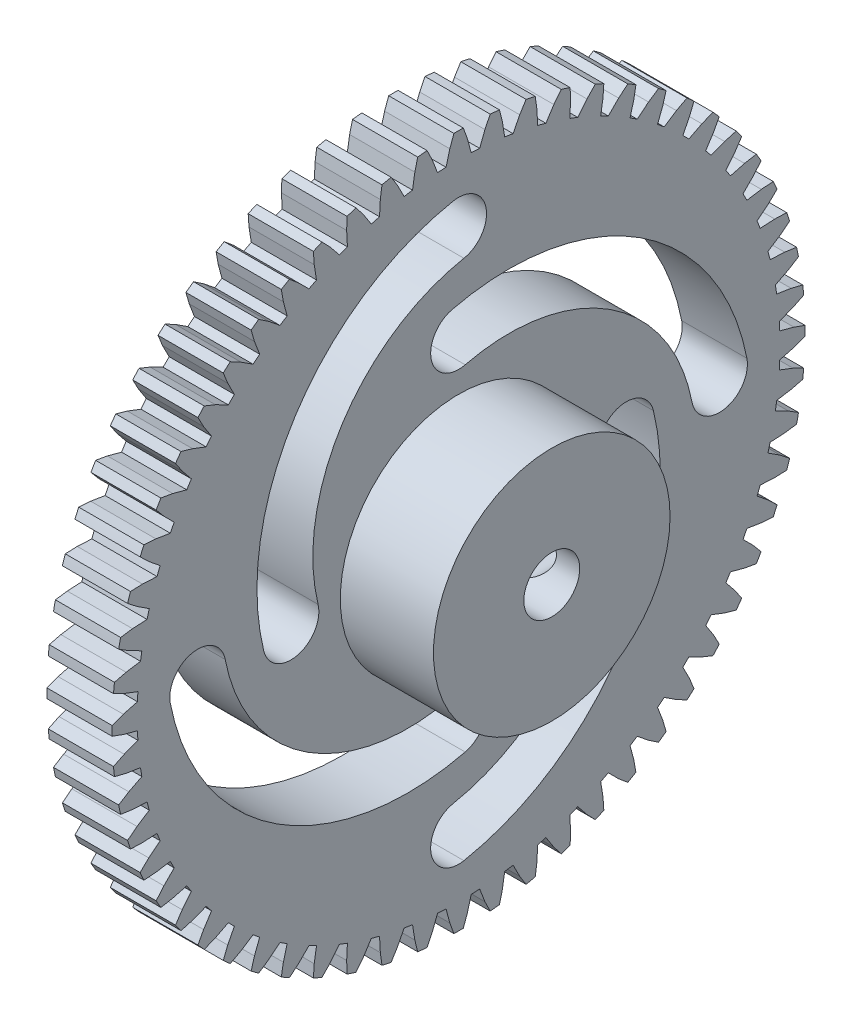
SolidWorks part; units mm, degrees
ref_plane "Front Plane" through (0, 0, 0) normal (0, 0, 1) x (1, 0, 0)
ref_plane "Top Plane" through (0, 0, 0) normal (0, 1, 0) x (1, 0, 0)
ref_plane "Right Plane" through (0, 0, 0) normal (1, 0, 0) x (0, 0, -1)
ref_plane "Plane1" through (6, 0, 0) normal (1, 0, 0) x (0, 0, -1)
sketch "Sketch1" plane through (6, 0, 0) normal (1, 0, 0) x (0, 0, -1)
  line L0 (1.6942, 18.5227) -> (1.4122, 17.9445)
  line L1 (-0.2512, 18.5983) -> (-0.4712, 17.9938)
  line L2 (-0.4712, 17.9938) -> (-0.6741, 17.2368)
  line L3 (-1.1314, 17.2129) -> (-1.4122, 17.9445)
  line L4 (-1.4122, 17.9445) -> (-1.6942, 18.5227)
  line L5 (1.4122, 17.9445) -> (1.1314, 17.2129)
  line L6 (0.6741, 17.2368) -> (0.4712, 17.9938)
  line L7 (0.4712, 17.9938) -> (0.2512, 18.5983)
  line L8 (3.6211, 18.2441) -> (3.2802, 17.6986)
  line L9 (3.2802, 17.6986) -> (2.9244, 17.0003)
  line L10 (2.4721, 17.0719) -> (2.3495, 17.846)
  line L11 (2.3495, 17.846) -> (2.1939, 18.4702)
  line L12 (5.5083, 17.7657) -> (5.1122, 17.2588)
  line L13 (5.1122, 17.2588) -> (4.6854, 16.6015)
  line L14 (4.2431, 16.72) -> (4.2021, 17.5026)
  line L15 (4.2021, 17.5026) -> (4.1125, 18.1397)
  line L16 (7.3351, 17.0926) -> (6.8883, 16.6299)
  line L17 (6.8883, 16.6299) -> (6.395, 16.0208)
  line L18 (5.9676, 16.1849) -> (6.0086, 16.9675)
  line L19 (6.0086, 16.9675) -> (5.9861, 17.6104)
  line L20 (9.0816, 16.2322) -> (8.5888, 15.8187)
  line L21 (8.5888, 15.8187) -> (8.0346, 15.2646)
  line L22 (7.6266, 15.4725) -> (7.7492, 16.2465)
  line L23 (7.7492, 16.2465) -> (7.7941, 16.8882)
  line L24 (10.7286, 15.194) -> (10.1953, 14.8343)
  line L25 (10.1953, 14.8343) -> (9.5862, 14.3411)
  line L26 (9.2022, 14.5905) -> (9.405, 15.3475)
  line L27 (9.405, 15.3475) -> (9.5167, 15.981)
  line L28 (12.258, 13.9893) -> (11.69, 13.6873)
  line L29 (11.69, 13.6873) -> (11.0327, 13.2605)
  line L30 (10.6769, 13.5487) -> (10.9577, 14.2803)
  line L31 (10.9577, 14.2803) -> (11.1351, 14.8987)
  line L32 (13.6531, 12.6314) -> (13.0567, 12.3904)
  line L33 (13.0567, 12.3904) -> (12.3584, 12.0346)
  line L34 (12.0346, 12.3584) -> (12.3904, 13.0567)
  line L35 (12.3904, 13.0567) -> (12.6314, 13.6531)
  line L36 (14.8987, 11.1351) -> (14.2803, 10.9577)
  line L37 (14.2803, 10.9577) -> (13.5487, 10.6769)
  line L38 (13.2605, 11.0327) -> (13.6873, 11.69)
  line L39 (13.6873, 11.69) -> (13.9893, 12.258)
  line L40 (15.981, 9.5167) -> (15.3475, 9.405)
  line L41 (15.3475, 9.405) -> (14.5905, 9.2022)
  line L42 (14.3411, 9.5862) -> (14.8343, 10.1953)
  line L43 (14.8343, 10.1953) -> (15.194, 10.7286)
  line L44 (16.8882, 7.7941) -> (16.2465, 7.7492)
  line L45 (16.2465, 7.7492) -> (15.4725, 7.6266)
  line L46 (15.2646, 8.0346) -> (15.8187, 8.5888)
  line L47 (15.8187, 8.5888) -> (16.2322, 9.0816)
  line L48 (17.6104, 5.9861) -> (16.9675, 6.0086)
  line L49 (16.9675, 6.0086) -> (16.1849, 5.9676)
  line L50 (16.0208, 6.395) -> (16.6299, 6.8883)
  line L51 (16.6299, 6.8883) -> (17.0926, 7.3351)
  line L52 (18.1397, 4.1125) -> (17.5026, 4.2021)
  line L53 (17.5026, 4.2021) -> (16.72, 4.2431)
  line L54 (16.6015, 4.6854) -> (17.2588, 5.1122)
  line L55 (17.2588, 5.1122) -> (17.7657, 5.5083)
  line L56 (18.4702, 2.1939) -> (17.846, 2.3495)
  line L57 (17.846, 2.3495) -> (17.0719, 2.4721)
  line L58 (17.0003, 2.9244) -> (17.6986, 3.2802)
  line L59 (17.6986, 3.2802) -> (18.2441, 3.6211)
  line L60 (18.5983, 0.2512) -> (17.9938, 0.4712)
  line L61 (17.9938, 0.4712) -> (17.2368, 0.6741)
  line L62 (17.2129, 1.1314) -> (17.9445, 1.4122)
  line L63 (17.9445, 1.4122) -> (18.5227, 1.6942)
  line L64 (18.5227, -1.6942) -> (17.9445, -1.4122)
  line L65 (17.9445, -1.4122) -> (17.2129, -1.1314)
  line L66 (17.2368, -0.6741) -> (17.9938, -0.4712)
  line L67 (17.9938, -0.4712) -> (18.5983, -0.2512)
  line L68 (18.2441, -3.6211) -> (17.6986, -3.2802)
  line L69 (17.6986, -3.2802) -> (17.0003, -2.9244)
  line L70 (17.0719, -2.4721) -> (17.846, -2.3495)
  line L71 (17.846, -2.3495) -> (18.4702, -2.1939)
  line L72 (17.7657, -5.5083) -> (17.2588, -5.1122)
  line L73 (17.2588, -5.1122) -> (16.6015, -4.6854)
  line L74 (16.72, -4.2431) -> (17.5026, -4.2021)
  line L75 (17.5026, -4.2021) -> (18.1397, -4.1125)
  line L76 (17.0926, -7.3351) -> (16.6299, -6.8883)
  line L77 (16.6299, -6.8883) -> (16.0208, -6.395)
  line L78 (16.1849, -5.9676) -> (16.9675, -6.0086)
  line L79 (16.9675, -6.0086) -> (17.6104, -5.9861)
  line L80 (16.2322, -9.0816) -> (15.8187, -8.5888)
  line L81 (15.8187, -8.5888) -> (15.2646, -8.0346)
  line L82 (15.4725, -7.6266) -> (16.2465, -7.7492)
  line L83 (16.2465, -7.7492) -> (16.8882, -7.7941)
  line L84 (15.194, -10.7286) -> (14.8343, -10.1953)
  line L85 (14.8343, -10.1953) -> (14.3411, -9.5862)
  line L86 (14.5905, -9.2022) -> (15.3475, -9.405)
  line L87 (15.3475, -9.405) -> (15.981, -9.5167)
  line L88 (13.9893, -12.258) -> (13.6873, -11.69)
  line L89 (13.6873, -11.69) -> (13.2605, -11.0327)
  line L90 (13.5487, -10.6769) -> (14.2803, -10.9577)
  line L91 (14.2803, -10.9577) -> (14.8987, -11.1351)
  line L92 (12.6314, -13.6531) -> (12.3904, -13.0567)
  line L93 (12.3904, -13.0567) -> (12.0346, -12.3584)
  line L94 (12.3584, -12.0346) -> (13.0567, -12.3904)
  line L95 (13.0567, -12.3904) -> (13.6531, -12.6314)
  line L96 (11.1351, -14.8987) -> (10.9577, -14.2803)
  line L97 (10.9577, -14.2803) -> (10.6769, -13.5487)
  line L98 (11.0327, -13.2605) -> (11.69, -13.6873)
  line L99 (11.69, -13.6873) -> (12.258, -13.9893)
  line L100 (9.5167, -15.981) -> (9.405, -15.3475)
  line L101 (9.405, -15.3475) -> (9.2022, -14.5905)
  line L102 (9.5862, -14.3411) -> (10.1953, -14.8343)
  line L103 (10.1953, -14.8343) -> (10.7286, -15.194)
  line L104 (7.7941, -16.8882) -> (7.7492, -16.2465)
  line L105 (7.7492, -16.2465) -> (7.6266, -15.4725)
  line L106 (8.0346, -15.2646) -> (8.5888, -15.8187)
  line L107 (8.5888, -15.8187) -> (9.0816, -16.2322)
  line L108 (5.9861, -17.6104) -> (6.0086, -16.9675)
  line L109 (6.0086, -16.9675) -> (5.9676, -16.1849)
  line L110 (6.395, -16.0208) -> (6.8883, -16.6299)
  line L111 (6.8883, -16.6299) -> (7.3351, -17.0926)
  line L112 (4.1125, -18.1397) -> (4.2021, -17.5026)
  line L113 (4.2021, -17.5026) -> (4.2431, -16.72)
  line L114 (4.6854, -16.6015) -> (5.1122, -17.2588)
  line L115 (5.1122, -17.2588) -> (5.5083, -17.7657)
  line L116 (2.1939, -18.4702) -> (2.3495, -17.846)
  line L117 (2.3495, -17.846) -> (2.4721, -17.0719)
  line L118 (2.9244, -17.0003) -> (3.2802, -17.6986)
  line L119 (3.2802, -17.6986) -> (3.6211, -18.2441)
  line L120 (0.2512, -18.5983) -> (0.4712, -17.9938)
  line L121 (0.4712, -17.9938) -> (0.6741, -17.2368)
  line L122 (1.1314, -17.2129) -> (1.4122, -17.9445)
  line L123 (1.4122, -17.9445) -> (1.6942, -18.5227)
  line L124 (-1.6942, -18.5227) -> (-1.4122, -17.9445)
  line L125 (-1.4122, -17.9445) -> (-1.1314, -17.2129)
  line L126 (-0.6741, -17.2368) -> (-0.4712, -17.9938)
  line L127 (-0.4712, -17.9938) -> (-0.2512, -18.5983)
  line L128 (-3.6211, -18.2441) -> (-3.2802, -17.6986)
  line L129 (-3.2802, -17.6986) -> (-2.9244, -17.0003)
  line L130 (-2.4721, -17.0719) -> (-2.3495, -17.846)
  line L131 (-2.3495, -17.846) -> (-2.1939, -18.4702)
  line L132 (-5.5083, -17.7657) -> (-5.1122, -17.2588)
  line L133 (-5.1122, -17.2588) -> (-4.6854, -16.6015)
  line L134 (-4.2431, -16.72) -> (-4.2021, -17.5026)
  line L135 (-4.2021, -17.5026) -> (-4.1125, -18.1397)
  line L136 (-7.3351, -17.0926) -> (-6.8883, -16.6299)
  line L137 (-6.8883, -16.6299) -> (-6.395, -16.0208)
  line L138 (-5.9676, -16.1849) -> (-6.0086, -16.9675)
  line L139 (-6.0086, -16.9675) -> (-5.9861, -17.6104)
  line L140 (-9.0816, -16.2322) -> (-8.5888, -15.8187)
  line L141 (-8.5888, -15.8187) -> (-8.0346, -15.2646)
  line L142 (-7.6266, -15.4725) -> (-7.7492, -16.2465)
  line L143 (-7.7492, -16.2465) -> (-7.7941, -16.8882)
  line L144 (-10.7286, -15.194) -> (-10.1953, -14.8343)
  line L145 (-10.1953, -14.8343) -> (-9.5862, -14.3411)
  line L146 (-9.2022, -14.5905) -> (-9.405, -15.3475)
  line L147 (-9.405, -15.3475) -> (-9.5167, -15.981)
  line L148 (-12.258, -13.9893) -> (-11.69, -13.6873)
  line L149 (-11.69, -13.6873) -> (-11.0327, -13.2605)
  line L150 (-10.6769, -13.5487) -> (-10.9577, -14.2803)
  line L151 (-10.9577, -14.2803) -> (-11.1351, -14.8987)
  line L152 (-13.6531, -12.6314) -> (-13.0567, -12.3904)
  line L153 (-13.0567, -12.3904) -> (-12.3584, -12.0346)
  line L154 (-12.0346, -12.3584) -> (-12.3904, -13.0567)
  line L155 (-12.3904, -13.0567) -> (-12.6314, -13.6531)
  line L156 (-14.8987, -11.1351) -> (-14.2803, -10.9577)
  line L157 (-14.2803, -10.9577) -> (-13.5487, -10.6769)
  line L158 (-13.2605, -11.0327) -> (-13.6873, -11.69)
  line L159 (-13.6873, -11.69) -> (-13.9893, -12.258)
  line L160 (-15.981, -9.5167) -> (-15.3475, -9.405)
  line L161 (-15.3475, -9.405) -> (-14.5905, -9.2022)
  line L162 (-14.3411, -9.5862) -> (-14.8343, -10.1953)
  line L163 (-14.8343, -10.1953) -> (-15.194, -10.7286)
  line L164 (-16.8882, -7.7941) -> (-16.2465, -7.7492)
  line L165 (-16.2465, -7.7492) -> (-15.4725, -7.6266)
  line L166 (-15.2646, -8.0346) -> (-15.8187, -8.5888)
  line L167 (-15.8187, -8.5888) -> (-16.2322, -9.0816)
  line L168 (-17.6104, -5.9861) -> (-16.9675, -6.0086)
  line L169 (-16.9675, -6.0086) -> (-16.1849, -5.9676)
  line L170 (-16.0208, -6.395) -> (-16.6299, -6.8883)
  line L171 (-16.6299, -6.8883) -> (-17.0926, -7.3351)
  line L172 (-18.1397, -4.1125) -> (-17.5026, -4.2021)
  line L173 (-17.5026, -4.2021) -> (-16.72, -4.2431)
  line L174 (-16.6015, -4.6854) -> (-17.2588, -5.1122)
  line L175 (-17.2588, -5.1122) -> (-17.7657, -5.5083)
  line L176 (-18.4702, -2.1939) -> (-17.846, -2.3495)
  line L177 (-17.846, -2.3495) -> (-17.0719, -2.4721)
  line L178 (-17.0003, -2.9244) -> (-17.6986, -3.2802)
  line L179 (-17.6986, -3.2802) -> (-18.2441, -3.6211)
  line L180 (-18.5983, -0.2512) -> (-17.9938, -0.4712)
  line L181 (-17.9938, -0.4712) -> (-17.2368, -0.6741)
  line L182 (-17.2129, -1.1314) -> (-17.9445, -1.4122)
  line L183 (-17.9445, -1.4122) -> (-18.5227, -1.6942)
  line L184 (-18.5227, 1.6942) -> (-17.9445, 1.4122)
  line L185 (-17.9445, 1.4122) -> (-17.2129, 1.1314)
  line L186 (-17.2368, 0.6741) -> (-17.9938, 0.4712)
  line L187 (-17.9938, 0.4712) -> (-18.5983, 0.2512)
  line L188 (-18.2441, 3.6211) -> (-17.6986, 3.2802)
  line L189 (-17.6986, 3.2802) -> (-17.0003, 2.9244)
  line L190 (-17.0719, 2.4721) -> (-17.846, 2.3495)
  line L191 (-17.846, 2.3495) -> (-18.4702, 2.1939)
  line L192 (-17.7657, 5.5083) -> (-17.2588, 5.1122)
  line L193 (-17.2588, 5.1122) -> (-16.6015, 4.6854)
  line L194 (-16.72, 4.2431) -> (-17.5026, 4.2021)
  line L195 (-17.5026, 4.2021) -> (-18.1397, 4.1125)
  line L196 (-17.0926, 7.3351) -> (-16.6299, 6.8883)
  line L197 (-16.6299, 6.8883) -> (-16.0208, 6.395)
  line L198 (-16.1849, 5.9676) -> (-16.9675, 6.0086)
  line L199 (-16.9675, 6.0086) -> (-17.6104, 5.9861)
  line L200 (-16.2322, 9.0816) -> (-15.8187, 8.5888)
  line L201 (-15.8187, 8.5888) -> (-15.2646, 8.0346)
  line L202 (-15.4725, 7.6266) -> (-16.2465, 7.7492)
  line L203 (-16.2465, 7.7492) -> (-16.8882, 7.7941)
  line L204 (-15.194, 10.7286) -> (-14.8343, 10.1953)
  line L205 (-14.8343, 10.1953) -> (-14.3411, 9.5862)
  line L206 (-14.5905, 9.2022) -> (-15.3475, 9.405)
  line L207 (-15.3475, 9.405) -> (-15.981, 9.5167)
  line L208 (-13.9893, 12.258) -> (-13.6873, 11.69)
  line L209 (-13.6873, 11.69) -> (-13.2605, 11.0327)
  line L210 (-13.5487, 10.6769) -> (-14.2803, 10.9577)
  line L211 (-14.2803, 10.9577) -> (-14.8987, 11.1351)
  line L212 (-12.6314, 13.6531) -> (-12.3904, 13.0567)
  line L213 (-12.3904, 13.0567) -> (-12.0346, 12.3584)
  line L214 (-12.3584, 12.0346) -> (-13.0567, 12.3904)
  line L215 (-13.0567, 12.3904) -> (-13.6531, 12.6314)
  line L216 (-11.1351, 14.8987) -> (-10.9577, 14.2803)
  line L217 (-10.9577, 14.2803) -> (-10.6769, 13.5487)
  line L218 (-11.0327, 13.2605) -> (-11.69, 13.6873)
  line L219 (-11.69, 13.6873) -> (-12.258, 13.9893)
  line L220 (-9.5167, 15.981) -> (-9.405, 15.3475)
  line L221 (-9.405, 15.3475) -> (-9.2022, 14.5905)
  line L222 (-9.5862, 14.3411) -> (-10.1953, 14.8343)
  line L223 (-10.1953, 14.8343) -> (-10.7286, 15.194)
  line L224 (-7.7941, 16.8882) -> (-7.7492, 16.2465)
  line L225 (-7.7492, 16.2465) -> (-7.6266, 15.4725)
  line L226 (-8.0346, 15.2646) -> (-8.5888, 15.8187)
  line L227 (-8.5888, 15.8187) -> (-9.0816, 16.2322)
  line L228 (-5.9861, 17.6104) -> (-6.0086, 16.9675)
  line L229 (-6.0086, 16.9675) -> (-5.9676, 16.1849)
  line L230 (-6.395, 16.0208) -> (-6.8883, 16.6299)
  line L231 (-6.8883, 16.6299) -> (-7.3351, 17.0926)
  line L232 (-4.1125, 18.1397) -> (-4.2021, 17.5026)
  line L233 (-4.2021, 17.5026) -> (-4.2431, 16.72)
  line L234 (-4.6854, 16.6015) -> (-5.1122, 17.2588)
  line L235 (-5.1122, 17.2588) -> (-5.5083, 17.7657)
  line L236 (-2.1939, 18.4702) -> (-2.3495, 17.846)
  line L237 (-2.3495, 17.846) -> (-2.4721, 17.0719)
  line L238 (-2.9244, 17.0003) -> (-3.2802, 17.6986)
  line L239 (-3.2802, 17.6986) -> (-3.6211, 18.2441)
  arc A0 (-3.6211, 18.2441) -> (-0.2512, 18.5983) centre (0, 0) ccw construction
  arc A1 (-0.6741, 17.2368) -> (-1.1314, 17.2129) centre (0, 0) ccw
  arc A2 (-1.6942, 18.5227) -> (-2.1939, 18.4702) centre (0, 0) ccw
  arc A3 (1.1314, 17.2129) -> (0.6741, 17.2368) centre (0, 0) ccw
  arc A4 (0.2512, 18.5983) -> (-0.2512, 18.5983) centre (0, 0) ccw
  arc A5 (2.9244, 17.0003) -> (2.4721, 17.0719) centre (0, 0) ccw
  arc A6 (2.1939, 18.4702) -> (1.6942, 18.5227) centre (0, 0) ccw
  arc A7 (4.6854, 16.6015) -> (4.2431, 16.72) centre (0, 0) ccw
  arc A8 (4.1125, 18.1397) -> (3.6211, 18.2441) centre (0, 0) ccw
  arc A9 (6.395, 16.0208) -> (5.9676, 16.1849) centre (0, 0) ccw
  arc A10 (5.9861, 17.6104) -> (5.5083, 17.7657) centre (0, 0) ccw
  arc A11 (8.0346, 15.2646) -> (7.6266, 15.4725) centre (0, 0) ccw
  arc A12 (7.7941, 16.8882) -> (7.3351, 17.0926) centre (0, 0) ccw
  arc A13 (9.5862, 14.3411) -> (9.2022, 14.5905) centre (0, 0) ccw
  arc A14 (9.5167, 15.981) -> (9.0816, 16.2322) centre (0, 0) ccw
  arc A15 (11.0327, 13.2605) -> (10.6769, 13.5487) centre (0, 0) ccw
  arc A16 (11.1351, 14.8987) -> (10.7286, 15.194) centre (0, 0) ccw
  arc A17 (12.3584, 12.0346) -> (12.0346, 12.3584) centre (0, 0) ccw
  arc A18 (12.6314, 13.6531) -> (12.258, 13.9893) centre (0, 0) ccw
  arc A19 (13.5487, 10.6769) -> (13.2605, 11.0327) centre (0, 0) ccw
  arc A20 (13.9893, 12.258) -> (13.6531, 12.6314) centre (0, 0) ccw
  arc A21 (14.5905, 9.2022) -> (14.3411, 9.5862) centre (0, 0) ccw
  arc A22 (15.194, 10.7286) -> (14.8987, 11.1351) centre (0, 0) ccw
  arc A23 (15.4725, 7.6266) -> (15.2646, 8.0346) centre (0, 0) ccw
  arc A24 (16.2322, 9.0816) -> (15.981, 9.5167) centre (0, 0) ccw
  arc A25 (16.1849, 5.9676) -> (16.0208, 6.395) centre (0, 0) ccw
  arc A26 (17.0926, 7.3351) -> (16.8882, 7.7941) centre (0, 0) ccw
  arc A27 (16.72, 4.2431) -> (16.6015, 4.6854) centre (0, 0) ccw
  arc A28 (17.7657, 5.5083) -> (17.6104, 5.9861) centre (0, 0) ccw
  arc A29 (17.0719, 2.4721) -> (17.0003, 2.9244) centre (0, 0) ccw
  arc A30 (18.2441, 3.6211) -> (18.1397, 4.1125) centre (0, 0) ccw
  arc A31 (17.2368, 0.6741) -> (17.2129, 1.1314) centre (0, 0) ccw
  arc A32 (18.5227, 1.6942) -> (18.4702, 2.1939) centre (0, 0) ccw
  arc A33 (17.2129, -1.1314) -> (17.2368, -0.6741) centre (0, 0) ccw
  arc A34 (18.5983, -0.2512) -> (18.5983, 0.2512) centre (0, 0) ccw
  arc A35 (17.0003, -2.9244) -> (17.0719, -2.4721) centre (0, 0) ccw
  arc A36 (18.4702, -2.1939) -> (18.5227, -1.6942) centre (0, 0) ccw
  arc A37 (16.6015, -4.6854) -> (16.72, -4.2431) centre (0, 0) ccw
  arc A38 (18.1397, -4.1125) -> (18.2441, -3.6211) centre (0, 0) ccw
  arc A39 (16.0208, -6.395) -> (16.1849, -5.9676) centre (0, 0) ccw
  arc A40 (17.6104, -5.9861) -> (17.7657, -5.5083) centre (0, 0) ccw
  arc A41 (15.2646, -8.0346) -> (15.4725, -7.6266) centre (0, 0) ccw
  arc A42 (16.8882, -7.7941) -> (17.0926, -7.3351) centre (0, 0) ccw
  arc A43 (14.3411, -9.5862) -> (14.5905, -9.2022) centre (0, 0) ccw
  arc A44 (15.981, -9.5167) -> (16.2322, -9.0816) centre (0, 0) ccw
  arc A45 (13.2605, -11.0327) -> (13.5487, -10.6769) centre (0, 0) ccw
  arc A46 (14.8987, -11.1351) -> (15.194, -10.7286) centre (0, 0) ccw
  arc A47 (12.0346, -12.3584) -> (12.3584, -12.0346) centre (0, 0) ccw
  arc A48 (13.6531, -12.6314) -> (13.9893, -12.258) centre (0, 0) ccw
  arc A49 (10.6769, -13.5487) -> (11.0327, -13.2605) centre (0, 0) ccw
  arc A50 (12.258, -13.9893) -> (12.6314, -13.6531) centre (0, 0) ccw
  arc A51 (9.2022, -14.5905) -> (9.5862, -14.3411) centre (0, 0) ccw
  arc A52 (10.7286, -15.194) -> (11.1351, -14.8987) centre (0, 0) ccw
  arc A53 (7.6266, -15.4725) -> (8.0346, -15.2646) centre (0, 0) ccw
  arc A54 (9.0816, -16.2322) -> (9.5167, -15.981) centre (0, 0) ccw
  arc A55 (5.9676, -16.1849) -> (6.395, -16.0208) centre (0, 0) ccw
  arc A56 (7.3351, -17.0926) -> (7.7941, -16.8882) centre (0, 0) ccw
  arc A57 (4.2431, -16.72) -> (4.6854, -16.6015) centre (0, 0) ccw
  arc A58 (5.5083, -17.7657) -> (5.9861, -17.6104) centre (0, 0) ccw
  arc A59 (2.4721, -17.0719) -> (2.9244, -17.0003) centre (0, 0) ccw
  arc A60 (3.6211, -18.2441) -> (4.1125, -18.1397) centre (0, 0) ccw
  arc A61 (0.6741, -17.2368) -> (1.1314, -17.2129) centre (0, 0) ccw
  arc A62 (1.6942, -18.5227) -> (2.1939, -18.4702) centre (0, 0) ccw
  arc A63 (-1.1314, -17.2129) -> (-0.6741, -17.2368) centre (0, 0) ccw
  arc A64 (-0.2512, -18.5983) -> (0.2512, -18.5983) centre (0, 0) ccw
  arc A65 (-2.9244, -17.0003) -> (-2.4721, -17.0719) centre (0, 0) ccw
  arc A66 (-2.1939, -18.4702) -> (-1.6942, -18.5227) centre (0, 0) ccw
  arc A67 (-4.6854, -16.6015) -> (-4.2431, -16.72) centre (0, 0) ccw
  arc A68 (-4.1125, -18.1397) -> (-3.6211, -18.2441) centre (0, 0) ccw
  arc A69 (-6.395, -16.0208) -> (-5.9676, -16.1849) centre (0, 0) ccw
  arc A70 (-5.9861, -17.6104) -> (-5.5083, -17.7657) centre (0, 0) ccw
  arc A71 (-8.0346, -15.2646) -> (-7.6266, -15.4725) centre (0, 0) ccw
  arc A72 (-7.7941, -16.8882) -> (-7.3351, -17.0926) centre (0, 0) ccw
  arc A73 (-9.5862, -14.3411) -> (-9.2022, -14.5905) centre (0, 0) ccw
  arc A74 (-9.5167, -15.981) -> (-9.0816, -16.2322) centre (0, 0) ccw
  arc A75 (-11.0327, -13.2605) -> (-10.6769, -13.5487) centre (0, 0) ccw
  arc A76 (-11.1351, -14.8987) -> (-10.7286, -15.194) centre (0, 0) ccw
  arc A77 (-12.3584, -12.0346) -> (-12.0346, -12.3584) centre (0, 0) ccw
  arc A78 (-12.6314, -13.6531) -> (-12.258, -13.9893) centre (0, 0) ccw
  arc A79 (-13.5487, -10.6769) -> (-13.2605, -11.0327) centre (0, 0) ccw
  arc A80 (-13.9893, -12.258) -> (-13.6531, -12.6314) centre (0, 0) ccw
  arc A81 (-14.5905, -9.2022) -> (-14.3411, -9.5862) centre (0, 0) ccw
  arc A82 (-15.194, -10.7286) -> (-14.8987, -11.1351) centre (0, 0) ccw
  arc A83 (-15.4725, -7.6266) -> (-15.2646, -8.0346) centre (0, 0) ccw
  arc A84 (-16.2322, -9.0816) -> (-15.981, -9.5167) centre (0, 0) ccw
  arc A85 (-16.1849, -5.9676) -> (-16.0208, -6.395) centre (0, 0) ccw
  arc A86 (-17.0926, -7.3351) -> (-16.8882, -7.7941) centre (0, 0) ccw
  arc A87 (-16.72, -4.2431) -> (-16.6015, -4.6854) centre (0, 0) ccw
  arc A88 (-17.7657, -5.5083) -> (-17.6104, -5.9861) centre (0, 0) ccw
  arc A89 (-17.0719, -2.4721) -> (-17.0003, -2.9244) centre (0, 0) ccw
  arc A90 (-18.2441, -3.6211) -> (-18.1397, -4.1125) centre (0, 0) ccw
  arc A91 (-17.2368, -0.6741) -> (-17.2129, -1.1314) centre (0, 0) ccw
  arc A92 (-18.5227, -1.6942) -> (-18.4702, -2.1939) centre (0, 0) ccw
  arc A93 (-17.2129, 1.1314) -> (-17.2368, 0.6741) centre (0, 0) ccw
  arc A94 (-18.5983, 0.2512) -> (-18.5983, -0.2512) centre (0, 0) ccw
  arc A95 (-17.0003, 2.9244) -> (-17.0719, 2.4721) centre (0, 0) ccw
  arc A96 (-18.4702, 2.1939) -> (-18.5227, 1.6942) centre (0, 0) ccw
  arc A97 (-16.6015, 4.6854) -> (-16.72, 4.2431) centre (0, 0) ccw
  arc A98 (-18.1397, 4.1125) -> (-18.2441, 3.6211) centre (0, 0) ccw
  arc A99 (-16.0208, 6.395) -> (-16.1849, 5.9676) centre (0, 0) ccw
  arc A100 (-17.6104, 5.9861) -> (-17.7657, 5.5083) centre (0, 0) ccw
  arc A101 (-15.2646, 8.0346) -> (-15.4725, 7.6266) centre (0, 0) ccw
  arc A102 (-16.8882, 7.7941) -> (-17.0926, 7.3351) centre (0, 0) ccw
  arc A103 (-14.3411, 9.5862) -> (-14.5905, 9.2022) centre (0, 0) ccw
  arc A104 (-15.981, 9.5167) -> (-16.2322, 9.0816) centre (0, 0) ccw
  arc A105 (-13.2605, 11.0327) -> (-13.5487, 10.6769) centre (0, 0) ccw
  arc A106 (-14.8987, 11.1351) -> (-15.194, 10.7286) centre (0, 0) ccw
  arc A107 (-12.0346, 12.3584) -> (-12.3584, 12.0346) centre (0, 0) ccw
  arc A108 (-13.6531, 12.6314) -> (-13.9893, 12.258) centre (0, 0) ccw
  arc A109 (-10.6769, 13.5487) -> (-11.0327, 13.2605) centre (0, 0) ccw
  arc A110 (-12.258, 13.9893) -> (-12.6314, 13.6531) centre (0, 0) ccw
  arc A111 (-9.2022, 14.5905) -> (-9.5862, 14.3411) centre (0, 0) ccw
  arc A112 (-10.7286, 15.194) -> (-11.1351, 14.8987) centre (0, 0) ccw
  arc A113 (-7.6266, 15.4725) -> (-8.0346, 15.2646) centre (0, 0) ccw
  arc A114 (-9.0816, 16.2322) -> (-9.5167, 15.981) centre (0, 0) ccw
  arc A115 (-5.9676, 16.1849) -> (-6.395, 16.0208) centre (0, 0) ccw
  arc A116 (-7.3351, 17.0926) -> (-7.7941, 16.8882) centre (0, 0) ccw
  arc A117 (-4.2431, 16.72) -> (-4.6854, 16.6015) centre (0, 0) ccw
  arc A118 (-5.5083, 17.7657) -> (-5.9861, 17.6104) centre (0, 0) ccw
  arc A119 (-2.4721, 17.0719) -> (-2.9244, 17.0003) centre (0, 0) ccw
  arc A120 (-3.6211, 18.2441) -> (-4.1125, 18.1397) centre (0, 0) ccw
  point P424 (0, 0)
  dimension "D1" = 60
extrude "Boss-Extrude1" add sketch "Sketch1" against normal blind 3.5
sketch "Sketch3" plane through (6, 0, 0) normal (1, 0, 0) x (0, 0, -1)
  circle A0 centre (0, 0) radius 6.35
  dimension "D1" = 12.7
extrude "Boss-Extrude2" add sketch "Sketch3" along normal blind 5
hole_wizard "Ø3.0mm Clearance Dowel Hole1" positions "Sketch9" profile "Sketch8" hole size "Ø3.0" standard "ANSI Metric" end condition through all
sketch "Sketch9" plane through (11, 0, 0) normal (1, 0, 0) x (0, 0, -1)
  point P0 (0, 0)
sketch "Sketch8" plane through (11, 0, 0) normal (0, 1, 0) x (0, 0, -1)
  line L0 (0, 0) -> (0, 8.5)
  line L1 (0, 8.5) -> (1.5, 8.5)
  line L2 (1.5, 8.5) -> (1.5, 0)
  line L5 (1.5, 0) -> (0, 0)
  line L11 (0, -6.35) -> (0, 107.95) construction
  dimension "Thru Hole Dia." = 3
  dimension "Thru Hole Depth" = 8.5
sketch "Sketch10" plane through (6, 0, 0) normal (1, 0, 0) x (0, 0, -1)
  line L0 (0, 14) -> (0, 0) construction
  line L1 (0, 0) -> (-9, 0) construction
  arc A0 (0.2839, 12.5271) -> (-0.2839, 15.4729) centre (0, 14) ccw
  arc A1 (-10.4578, -0.3532) -> (-7.5422, 0.3532) centre (-9, 0) ccw
  arc A2 (-7.5422, 0.3532) -> (0.2839, 12.5271) centre (2.1766, 2.7079) cw
  arc A3 (-10.4578, -0.3532) -> (-0.2839, 15.4729) centre (2.1766, 2.7079) cw
  point P8 (0, 0)
  dimension "D2" = 3
  dimension "D4" = 14
  dimension "D5" = 9
  dimension "D6" = 13
  dimension "D1" = 90
extrude "Cut-Extrude5" cut sketch "Sketch10" against normal through all
pattern_circular "CirPattern3" count 4 every 90 about axis through (0, 0, 0) along (1, 0, 0) of "Cut-Extrude5"
sketch "Sketch11" plane through (0, 0, 0) normal (0, 0, 1) x (1, 0, 0)
  line L0 (11, -6.35) -> (11, 6.35) construction
  circle A0 centre (8.5, 0) radius 1.25
  point P2 (0, 0)
  dimension "D1" = 2.5
  dimension "D2" = 2.5
extrude "Cut-Extrude6" cut sketch "Sketch11" against normal blind 10 contours A0
